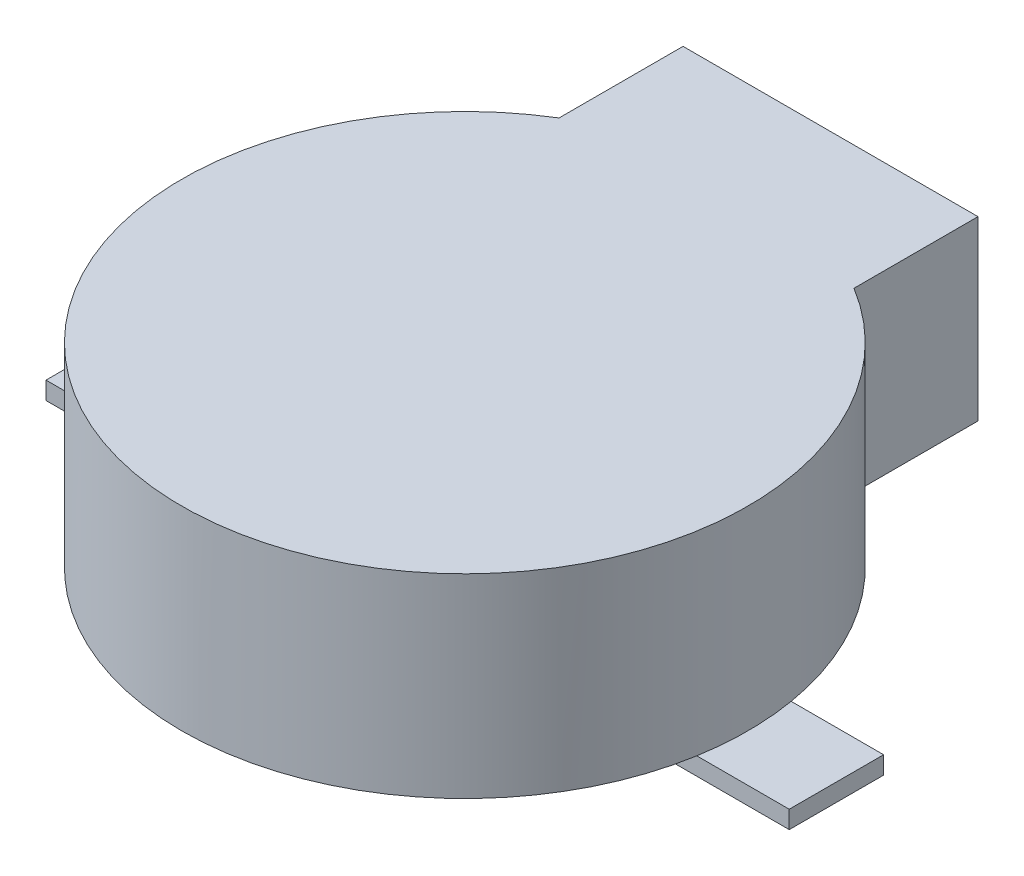
SolidWorks part; units mm, degrees
material "1060 Alloy"
ref_plane "Front Plane" through (0, 0, 0) normal (0, 0, 1) x (1, 0, 0)
ref_plane "Top Plane" through (0, 0, 0) normal (0, 1, 0) x (1, 0, 0)
ref_plane "Right Plane" through (0, 0, 0) normal (1, 0, 0) x (0, 0, -1)
sketch "Sketch1" plane through (0, 0, 0) normal (0, 1, 0) x (1, 0, 0)
  line L1 (-2.5, 4.0976) -> (2.5, 4.0976) construction
  line L2 (-2.5, 4.0976) -> (-2.5, 6.2)
  line L3 (-2.5, 6.2) -> (2.5, 6.2)
  line L4 (2.5, 4.0976) -> (2.5, 6.2)
  arc A0 (-2.5, 4.0976) -> (2.5, 4.0976) centre (0, 0) ccw
  dimension "D1" = 9.6
  dimension "D2" = 6.2
  dimension "D3" = 5
extrude "Boss-Extrude1" add sketch "Sketch1" along normal blind 3.3
sketch "Sketch2" plane through (0, 0, 0) normal (0, -1, 0) x (1, 0, 0)
  line L1 (-6.3, 0.8) -> (-2.8, 0.8)
  line L2 (-6.3, 0.8) -> (-6.3, -0.8)
  line L3 (-6.3, -0.8) -> (-2.8, -0.8)
  line L4 (-2.8, 0.8) -> (-2.8, -0.8)
  line L5 (2.8, 0.8) -> (6.3, 0.8)
  line L6 (2.8, 0.8) -> (2.8, -0.8)
  line L7 (2.8, -0.8) -> (6.3, -0.8)
  line L8 (6.3, 0.8) -> (6.3, -0.8)
  point P8 (-2.8, 0)
  dimension "D1" = 1.6
  dimension "D2" = 6.3
  dimension "D3" = 12.6
  dimension "D4" = 3.5
  dimension "D5" = 3.5
extrude "Boss-Extrude2" add sketch "Sketch2" along normal blind 0.3
sketch "Sketch3" plane through (0, 0, 0) normal (0, -1, 0) x (1, 0, 0)
  line L1 (2.5, -4.0976) -> (2.5, -6.2) construction
  line L2 (2.5, -6.2) -> (-2.5, -6.2) construction
  line L3 (-2.5, -6.2) -> (-2.5, -4.0976) construction
  line L4 (2.5, -4.0976) -> (2.5, -6.2)
  line L5 (2.5, -6.2) -> (-2.5, -6.2)
  line L6 (-2.5, -6.2) -> (-2.5, -4.0976)
  arc A0 (-4.7329, -0.8) -> (-2.5, -4.0976) centre (0, 0) ccw construction
  arc A1 (-2.5, -4.0976) -> (2.5, -4.0976) centre (0, 0) ccw
extrude "Cut-Extrude1" cut sketch "Sketch3" against normal blind 0.3
sketch "Sketch4" plane through (0, 0, -6.2) normal (0, 0, -1) x (-1, 0, 0)
  line L8 (-2, 0.8) -> (2, 0.8)
  line L9 (2, 0.8) -> (2, 2.8)
  line L10 (2, 2.8) -> (-2, 2.8)
  line L11 (-2, 2.8) -> (-2, 0.8)
  line L12 (-2, 0.8) -> (2, 0.8)
  line L13 (2, 0.8) -> (2, 2.8)
  line L14 (2, 2.8) -> (-2, 2.8)
  line L15 (-2, 2.8) -> (-2, 0.8)
  dimension "D1" = 0.5
extrude "Cut-Extrude2" cut sketch "Sketch4" against normal blind 3
